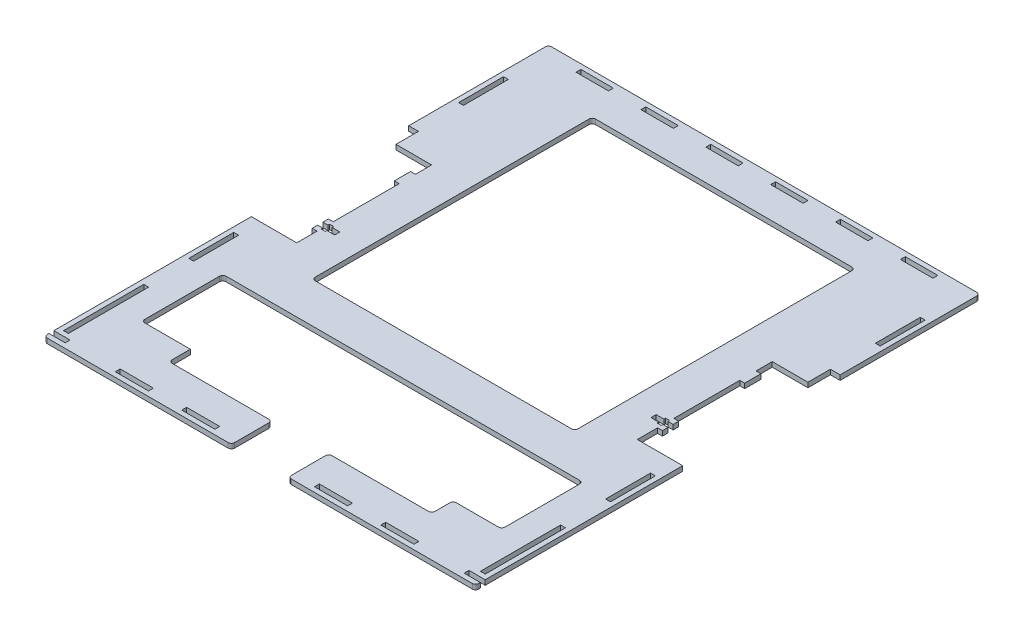
SolidWorks part; units mm, degrees
ref_plane "Front Plane" through (0, 0, 0) normal (0, 0, 1) x (1, 0, 0)
ref_plane "Top Plane" through (0, 0, 0) normal (0, 1, 0) x (1, 0, 0)
ref_plane "Right Plane" through (0, 0, 0) normal (1, 0, 0) x (0, 0, -1)
sketch "Sketch1" plane through (0, 0, 0) normal (0, 1, 0) x (1, 0, 0)
  line L0 (-127, 149.5) -> (-127, 155.5) construction
  line L1 (-133, -155.5) -> (133, -155.5)
  line L2 (-133, -155.5) -> (-133, 155.5)
  line L3 (-133, 155.5) -> (133, 155.5)
  line L4 (133, -155.5) -> (133, 155.5)
  line L5 (-133, -155.5) -> (133, 155.5) construction
  line L6 (-133, 155.5) -> (133, -155.5) construction
  line L7 (-130, -152.5) -> (130, -152.5) construction
  line L8 (-130, -152.5) -> (-130, 152.5) construction
  line L9 (-130, 152.5) -> (130, 152.5) construction
  line L10 (130, -152.5) -> (130, 152.5) construction
  line L11 (-130, -152.5) -> (130, 152.5) construction
  line L12 (-130, 152.5) -> (130, -152.5) construction
  line L13 (-127, -149.5) -> (127, -149.5) construction
  line L14 (-127, -149.5) -> (-127, 149.5) construction
  line L15 (-127, 149.5) -> (127, 149.5) construction
  line L16 (127, -149.5) -> (127, 149.5) construction
  line L17 (-127, -149.5) -> (127, 149.5) construction
  line L18 (-127, 149.5) -> (127, -149.5) construction
  line L19 (-127, 149.5) -> (-133, 149.5) construction
  line L20 (-130, 152.5) -> (-110, 152.5) construction
  line L21 (-110, 149.5) -> (-90, 149.5)
  line L22 (-110, 149.5) -> (-110, 152.5)
  line L23 (-110, 152.5) -> (-90, 152.5)
  line L24 (-90, 149.5) -> (-90, 152.5)
  line L25 (-110, 149.5) -> (-90, 152.5) construction
  line L26 (-110, 152.5) -> (-90, 149.5) construction
  line L27 (-30, 149.5) -> (-10, 149.5)
  line L28 (-30, 149.5) -> (-30, 152.5)
  line L29 (-30, 152.5) -> (-10, 152.5)
  line L30 (-10, 149.5) -> (-10, 152.5)
  line L31 (-30, 149.5) -> (-10, 152.5) construction
  line L32 (-30, 152.5) -> (-10, 149.5) construction
  line L33 (-70, 149.5) -> (-50, 149.5)
  line L34 (-70, 149.5) -> (-70, 152.5)
  line L35 (-70, 152.5) -> (-50, 152.5)
  line L36 (-50, 149.5) -> (-50, 152.5)
  line L37 (-70, 149.5) -> (-50, 152.5) construction
  line L38 (-70, 152.5) -> (-50, 149.5) construction
  line L39 (10, 149.5) -> (30, 149.5)
  line L40 (10, 149.5) -> (10, 152.5)
  line L41 (10, 152.5) -> (30, 152.5)
  line L42 (30, 149.5) -> (30, 152.5)
  line L43 (10, 149.5) -> (30, 152.5) construction
  line L44 (10, 152.5) -> (30, 149.5) construction
  line L45 (50, 149.5) -> (70, 149.5)
  line L46 (50, 149.5) -> (50, 152.5)
  line L47 (50, 152.5) -> (70, 152.5)
  line L48 (70, 149.5) -> (70, 152.5)
  line L49 (50, 149.5) -> (70, 152.5) construction
  line L50 (50, 152.5) -> (70, 149.5) construction
  line L51 (90, 149.5) -> (110, 149.5)
  line L52 (90, 149.5) -> (90, 152.5)
  line L53 (90, 152.5) -> (110, 152.5)
  line L54 (110, 149.5) -> (110, 152.5)
  line L55 (90, 149.5) -> (110, 152.5) construction
  line L56 (90, 152.5) -> (110, 149.5) construction
  line L57 (-90, 152.5) -> (-70, 152.5) construction
  line L58 (-50, 152.5) -> (-30, 152.5) construction
  line L59 (-10, 152.5) -> (10, 152.5) construction
  line L60 (30, 152.5) -> (50, 152.5) construction
  line L61 (70, 152.5) -> (90, 152.5) construction
  line L62 (110, 152.5) -> (130, 152.5) construction
  line L63 (10.2307, -149.5) -> (30.6922, -149.5) construction
  line L64 (-10.2308, -152.5) -> (10.2307, -152.5)
  line L65 (-10.2308, -152.5) -> (-10.2308, -149.5)
  line L66 (-10.2308, -149.5) -> (10.2307, -149.5)
  line L67 (10.2307, -152.5) -> (10.2307, -149.5)
  line L68 (-10.2308, -152.5) -> (10.2307, -149.5) construction
  line L69 (-10.2308, -149.5) -> (10.2307, -152.5) construction
  line L70 (30.6922, -152.5) -> (51.1537, -152.5)
  line L71 (30.6922, -152.5) -> (30.6922, -149.5)
  line L72 (30.6922, -149.5) -> (51.1537, -149.5)
  line L73 (51.1537, -152.5) -> (51.1537, -149.5)
  line L74 (30.6922, -152.5) -> (51.1537, -149.5) construction
  line L75 (30.6922, -149.5) -> (51.1537, -152.5) construction
  line L76 (92.0767, -152.5) -> (71.6152, -152.5)
  line L77 (92.0767, -152.5) -> (92.0767, -149.5)
  line L78 (92.0767, -149.5) -> (71.6152, -149.5)
  line L79 (71.6152, -152.5) -> (71.6152, -149.5)
  line L80 (92.0767, -152.5) -> (71.6152, -149.5) construction
  line L81 (92.0767, -149.5) -> (71.6152, -152.5) construction
  line L82 (-51.1538, -152.5) -> (-30.6923, -152.5)
  line L83 (-51.1538, -152.5) -> (-51.1538, -149.5)
  line L84 (-51.1538, -149.5) -> (-30.6923, -149.5)
  line L85 (-30.6923, -152.5) -> (-30.6923, -149.5)
  line L86 (-51.1538, -152.5) -> (-30.6923, -149.5) construction
  line L87 (-51.1538, -149.5) -> (-30.6923, -152.5) construction
  line L88 (-92.0768, -152.5) -> (-71.6153, -152.5)
  line L89 (-92.0768, -152.5) -> (-92.0768, -149.5)
  line L90 (-92.0768, -149.5) -> (-71.6153, -149.5)
  line L91 (-71.6153, -152.5) -> (-71.6153, -149.5)
  line L92 (-92.0768, -152.5) -> (-71.6153, -149.5) construction
  line L93 (-92.0768, -149.5) -> (-71.6153, -152.5) construction
  line L94 (51.1537, -149.5) -> (71.6152, -149.5) construction
  line L95 (-10.2308, -149.5) -> (-30.6923, -149.5) construction
  line L96 (-51.1538, -149.5) -> (-71.6153, -149.5) construction
  line L97 (128.5, -97.0455) -> (128.5, -69.3182) construction
  line L98 (133, -152.5) -> (123, -152.5)
  line L99 (133, -152.5) -> (133, -149.5)
  line L100 (133, -149.5) -> (123, -149.5)
  line L101 (123, -152.5) -> (123, -149.5)
  line L102 (133, -152.5) -> (123, -149.5) construction
  line L103 (133, -149.5) -> (123, -152.5) construction
  line L104 (-133, -152.5) -> (-123, -152.5)
  line L105 (-133, -152.5) -> (-133, -149.5)
  line L106 (-133, -149.5) -> (-123, -149.5)
  line L107 (-123, -152.5) -> (-123, -149.5)
  line L108 (-133, -152.5) -> (-123, -149.5) construction
  line L109 (-133, -149.5) -> (-123, -152.5) construction
  line L110 (127, -97.0455) -> (130, -97.0455)
  line L111 (127, -97.0455) -> (127, -146.5)
  line L112 (127, -146.5) -> (130, -146.5)
  line L113 (130, -97.0455) -> (130, -146.5)
  line L114 (127, -97.0455) -> (130, -146.5) construction
  line L115 (127, -146.5) -> (130, -97.0455) construction
  line L116 (127, -41.5909) -> (130, -41.5909)
  line L117 (127, -41.5909) -> (127, -69.3182)
  line L118 (127, -69.3182) -> (130, -69.3182)
  line L119 (130, -41.5909) -> (130, -69.3182)
  line L120 (127, -41.5909) -> (130, -69.3182) construction
  line L121 (127, -69.3182) -> (130, -41.5909) construction
  line L123 (127, 97.0454) -> (130, 97.0454)
  line L124 (127, 97.0454) -> (127, 124.7727)
  line L125 (127, 124.7727) -> (130, 124.7727)
  line L126 (130, 97.0454) -> (130, 124.7727)
  line L127 (127, 97.0454) -> (130, 124.7727) construction
  line L128 (127, 124.7727) -> (130, 97.0454) construction
  line L129 (127, 69.3181) -> (127, 55.4545)
  line L130 (127, 55.4545) -> (105, 55.4545)
  line L132 (105, -27.7273) -> (133, -27.7273)
  line L134 (130, 97.0454) -> (130, 69.3181) construction
  line L135 (105, 55.4545) -> (105, 45.4545)
  line L136 (105, 45.4545) -> (108, 45.4545)
  line L137 (108, 45.4545) -> (108, 35.4545)
  line L138 (108, 35.4545) -> (105, 35.4545)
  line L139 (105, 35.4545) -> (105, -5.2273)
  line L140 (105, -5.2273) -> (108, -5.2273)
  line L141 (108, -5.2273) -> (108, -15.2273)
  line L142 (108, -15.2273) -> (105, -15.2273)
  line L143 (105, -15.2273) -> (105, -27.7273)
  line L144 (127, 69.3181) -> (133, 69.3181)
  line L145 (133, 69.3181) -> (133, -27.7273)
  line L146 (0, -773.499) -> (0, 49226.501) construction
  line L147 (-127, -146.5) -> (-130, -146.5)
  line L148 (-130, -97.0455) -> (-130, -146.5)
  line L149 (-127, -97.0455) -> (-130, -97.0455)
  line L150 (-127, -97.0455) -> (-127, -146.5)
  line L151 (-127, -69.3182) -> (-130, -69.3182)
  line L152 (-130, -41.5909) -> (-130, -69.3182)
  line L153 (-127, -41.5909) -> (-130, -41.5909)
  line L154 (-127, -41.5909) -> (-127, -69.3182)
  line L155 (-127, 124.7727) -> (-130, 124.7727)
  line L156 (-130, 97.0454) -> (-130, 124.7727)
  line L157 (-127, 97.0454) -> (-130, 97.0454)
  line L158 (-127, 97.0454) -> (-127, 124.7727)
  line L159 (-105, -15.2273) -> (-105, -27.7273)
  line L160 (-108, -15.2273) -> (-105, -15.2273)
  line L161 (-108, -5.2273) -> (-108, -15.2273)
  line L162 (-105, -5.2273) -> (-108, -5.2273)
  line L163 (-105, 35.4545) -> (-105, -5.2273)
  line L164 (-108, 35.4545) -> (-105, 35.4545)
  line L165 (-108, 45.4545) -> (-108, 35.4545)
  line L166 (-105, 45.4545) -> (-108, 45.4545)
  line L167 (-105, 55.4545) -> (-105, 45.4545)
  line L168 (-127, 55.4545) -> (-105, 55.4545)
  line L169 (-127, 69.3181) -> (-127, 55.4545)
  line L170 (-127, 69.3181) -> (-133, 69.3181)
  line L171 (-133, 69.3181) -> (-133, -27.7273)
  line L172 (-105, -27.7273) -> (-133, -27.7273)
  line L174 (-81, -130.5) -> (81, -130.5)
  line L175 (-81, -130.5) -> (-81, 130.5)
  line L176 (-81, 130.5) -> (81, 130.5)
  line L177 (81, -130.5) -> (81, 130.5)
  line L178 (-81, -130.5) -> (81, 130.5) construction
  line L179 (-81, 130.5) -> (81, -130.5) construction
  point P0 (0, 0)
  point P6 (0, 0)
  point P11 (0, 0)
  point P16 (-100, 151)
  point P19 (-127, 152.5)
  point P21 (-130, 149.5)
  point P25 (-20, 151)
  point P30 (-60, 151)
  point P35 (20, 151)
  point P40 (60, 151)
  point P45 (100, 151)
  point P50 (128.5, -121.7728)
  point P51 (0, -151)
  point P56 (40.923, -151)
  point P61 (81.846, -151)
  point P66 (-40.923, -151)
  point P71 (-81.846, -151)
  point P76 (-128, -151)
  point P81 (128.5, 110.9091)
  point P82 (128.5, -55.4545)
  point P88 (128, -151)
  point P145 (0, 0)
  dimension "D1" = 266
  dimension "D2" = 311
  dimension "D3" = 6
  dimension "D4" = 20.4615
  dimension "D5" = 10
  dimension "D6" = 3
  dimension "D7" = 49.4545
  dimension "D8" = 27.7273
  dimension "D9" = 24.7273
  dimension "D10" = 13.8636
  dimension "D11" = 13.8636
  dimension "D12" = 22
  dimension "D13" = 10
  dimension "D14" = 40.6818
  dimension "D15" = 10
  dimension "D16" = 3
  dimension "D17" = 25
  dimension "D18" = 52
extrude "Boss-Extrude1" add sketch "Sketch1" along normal blind 3 contours L129 L144 L4 L3 L2 L106 L107 L104 L1 L98 L101 L100 L132 L143 L142 L141 L140 L139 L138 L137 L136 L135 L130 L126 L123 L124 L125 L91 L88 L89 L90 L85 L82 L83 L84 L73 L70 L71 L72 L67 L64 L65 L66
sketch "Sketch2" plane through (0, 3, 0) normal (0, 1, 0) x (1, 0, 0)
  line L0 (-108, -5.2273) -> (-108, -15.2273) construction
  line L1 (-97.5, -11.8273) -> (-108, -11.8273)
  line L2 (-97.5, -11.8273) -> (-97.5, -8.6273)
  line L3 (-97.5, -8.6273) -> (-108, -8.6273)
  line L4 (-108, -11.8273) -> (-108, -8.6273)
  line L5 (-97.5, -11.8273) -> (-108, -8.6273) construction
  line L6 (-97.5, -8.6273) -> (-108, -11.8273) construction
  line L7 (108, -5.2273) -> (108, -15.2273) construction
  line L8 (97.5, -11.8273) -> (108, -11.8273)
  line L9 (97.5, -11.8273) -> (97.5, -8.6273)
  line L10 (97.5, -8.6273) -> (108, -8.6273)
  line L11 (108, -11.8273) -> (108, -8.6273)
  line L12 (97.5, -11.8273) -> (108, -8.6273) construction
  line L13 (97.5, -8.6273) -> (108, -11.8273) construction
  line L14 (108, -10.2273) -> (104.825, -10.2273) construction
  line L15 (104.825, -12.8273) -> (102.325, -12.8273)
  line L16 (104.825, -12.8273) -> (104.825, -7.6273)
  line L17 (104.825, -7.6273) -> (102.325, -7.6273)
  line L18 (102.325, -12.8273) -> (102.325, -7.6273)
  line L19 (104.825, -12.8273) -> (102.325, -7.6273) construction
  line L20 (104.825, -7.6273) -> (102.325, -12.8273) construction
  line L21 (-102.325, -12.8273) -> (-104.825, -12.8273)
  line L22 (-102.325, -12.8273) -> (-102.325, -7.6273)
  line L23 (-102.325, -7.6273) -> (-104.825, -7.6273)
  line L24 (-104.825, -12.8273) -> (-104.825, -7.6273)
  line L25 (-102.325, -12.8273) -> (-104.825, -7.6273) construction
  line L26 (-102.325, -7.6273) -> (-104.825, -12.8273) construction
  line L27 (-108, -10.2273) -> (-104.825, -10.2273) construction
  point P0 (-102.75, -10.2273)
  point P7 (102.75, -10.2273)
  point P14 (103.575, -10.2273)
  point P19 (-103.575, -10.2273)
  point P24 (-108, -10.2273)
  point P25 (108, -10.2273)
  dimension "D1" = 3.2
  dimension "D2" = 10.5
  dimension "D3" = 2.5
  dimension "D4" = 5.2
  dimension "D5" = 3.175
extrude "Cut-Extrude1" cut sketch "Sketch2" against normal blind 10 contours L21 L24 L23 L22 | L1 L4 L3 L2 | L15 L18 L17 L16 | L8 L11 L10 L9
sketch "Sketch3" plane through (0, 3, 0) normal (0, 1, 0) x (1, 0, 0)
  line L0 (-81, -130.5) -> (81, -130.5) construction
  line L1 (-17.5, -155.5) -> (17.5, -155.5)
  line L2 (-17.5, -155.5) -> (-17.5, -130.5)
  line L3 (-17.5, -130.5) -> (17.5, -130.5)
  line L4 (17.5, -155.5) -> (17.5, -130.5)
  line L5 (-17.5, -155.5) -> (17.5, -130.5) construction
  line L6 (-17.5, -130.5) -> (17.5, -155.5) construction
  line L7 (-133, -155.5) -> (133, -155.5) construction
  line L8 (-81, -130.5) -> (-81, 130.5) construction
  line L9 (-111, -117.3182) -> (-81, -117.3182)
  line L10 (-111, -117.3182) -> (-111, -67.3182)
  line L11 (-111, -67.3182) -> (-81, -67.3182)
  line L12 (-81, -117.3182) -> (-81, -67.3182)
  line L13 (-111, -117.3182) -> (-81, -67.3182) construction
  line L14 (-111, -67.3182) -> (-81, -117.3182) construction
  line L15 (81, -130.5) -> (81, 130.5) construction
  line L16 (111, -117.3182) -> (81, -117.3182)
  line L17 (111, -117.3182) -> (111, -67.3182)
  line L18 (111, -67.3182) -> (81, -67.3182)
  line L19 (81, -117.3182) -> (81, -67.3182)
  line L20 (111, -117.3182) -> (81, -67.3182) construction
  line L21 (111, -67.3182) -> (81, -117.3182) construction
  line L22 (-133, -149.5) -> (-133, -27.7273) construction
  line L23 (-127, -69.3182) -> (-130, -69.3182) construction
  point P0 (0, -143)
  point P11 (-96, -92.3182)
  point P17 (96, -92.3182)
  point P24 (0, 0)
  dimension "D1" = 35
  dimension "D2" = 22
  dimension "D3" = 2
  dimension "D4" = 50
extrude "Cut-Extrude2" cut sketch "Sketch3" against normal through all both and the other way through all
sketch "Sketch4" plane through (0, 0, 0) normal (0, -1, 0) x (1, 0, 0)
  line L0 (-81, 67.3182) -> (-81, -130.5) construction
  line L1 (-81, 42.3182) -> (81, 42.3182)
  line L2 (-81, 42.3182) -> (-81, 67.3182)
  line L3 (-81, 67.3182) -> (81, 67.3182)
  line L4 (81, 42.3182) -> (81, 67.3182)
  line L5 (-81, 42.3182) -> (81, 67.3182) construction
  line L6 (-81, 67.3182) -> (81, 42.3182) construction
  point P0 (0, 54.8182)
  point P6 (-88, 23.78)
  dimension "D1" = 25
extrude "Boss-Extrude2" add sketch "Sketch4" against normal up to surface (3 mm away) up to face at (0, 3, 26.675)
fillet "Fillet1" radius 2 19 edges at (133, 1.5, 155.5) (-133, 1.5, 155.5) (133, 1.5, -155.5) (-133, 1.5, -155.5) (-17.5, 1.5, 130.5) (17.5, 1.5, 130.5) (17.5, 1.5, 155.5) (-17.5, 1.5, 155.5) (-81, 1.5, -130.5) (81, 1.5, -130.5) (111, 1.5, 67.3182) (111, 1.5, 117.3182) (81, 1.5, 117.3182) (81, 1.5, 130.5) (-111, 1.5, 117.3182) (-81, 1.5, 130.5) (-111, 1.5, 67.3182) (81, 1.5, 42.3182) (-81, 1.5, 42.3182)
